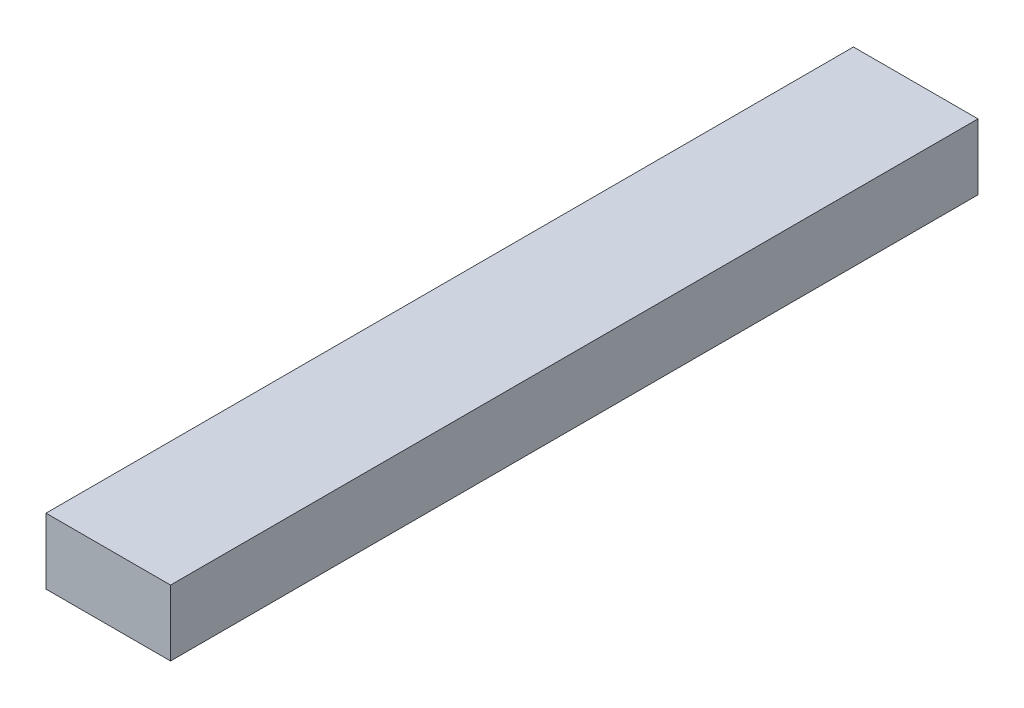
SolidWorks part; units mm, degrees
material "Cobalt"
ref_plane "Front Plane" through (0, 0, 0) normal (0, 0, 1) x (1, 0, 0)
ref_plane "Top Plane" through (0, 0, 0) normal (0, 1, 0) x (1, 0, 0)
ref_plane "Right Plane" through (0, 0, 0) normal (1, 0, 0) x (0, 0, -1)
sketch "Sketch1" plane through (0, 0, 0) normal (0, 1, 0) x (1, 0, 0)
  line L1 (0, 0) -> (19.7104, 0)
  line L2 (0, 0) -> (0, 127.7937)
  line L3 (0, 127.7937) -> (19.7104, 127.7937)
  line L4 (19.7104, 0) -> (19.7104, 127.7937)
  dimension "D1" = 127.7937
  dimension "D2" = 19.7104
extrude "Boss-Extrude1" add sketch "Sketch1" along normal blind 10.414
